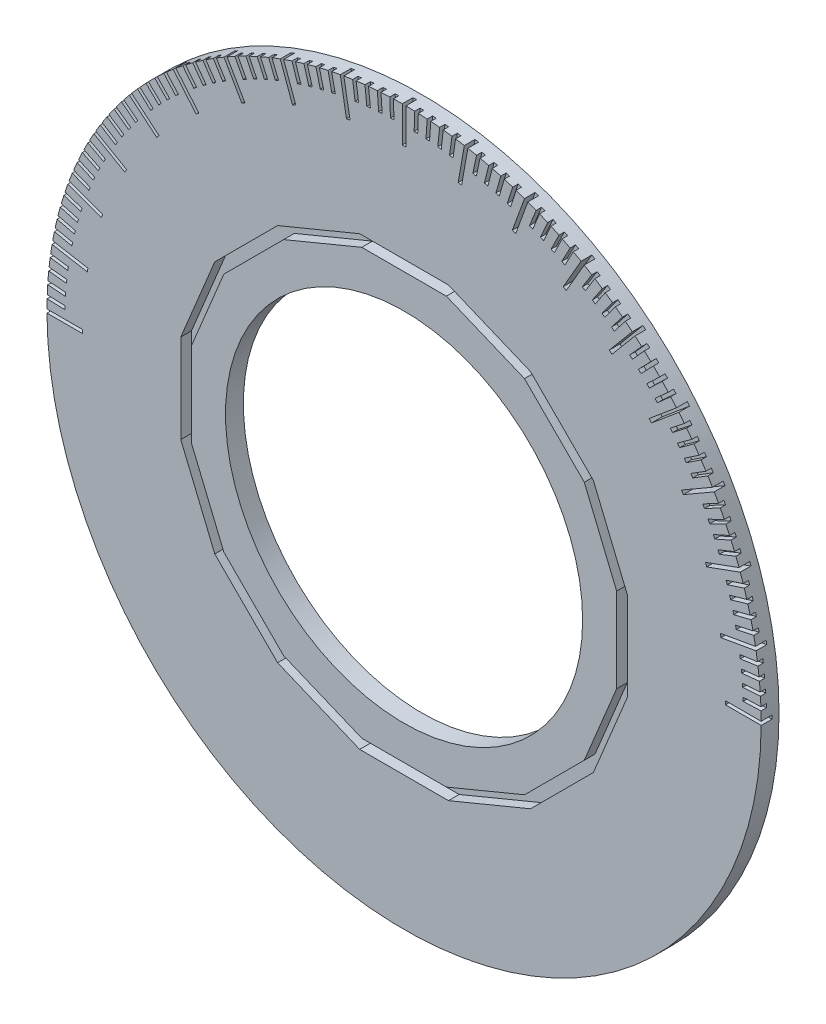
SolidWorks part; units mm, degrees
ref_plane "정면" through (0, 0, 0) normal (0, 0, 1) x (1, 0, 0)
ref_plane "윗면" through (0, 0, 0) normal (0, 1, 0) x (1, 0, 0)
ref_plane "우측면" through (0, 0, 0) normal (1, 0, 0) x (0, 0, -1)
sketch "스케치1" plane through (0, 0, 0) normal (0, 0, 1) x (1, 0, 0)
  circle A0 centre (0, 0) radius 40
  dimension "D1" = 80
extrude "보스-돌출1" add sketch "스케치1" along normal blind 2
sketch "스케치2" plane through (0, 0, 2) normal (0, 0, 1) x (1, 0, 0)
  line L103 (1.1, 0) -> (-1.1, 0) construction
  line L104 (21.2025, -14.167) -> (25.01, -4.9748)
  line L105 (25.01, -4.9748) -> (25.01, 4.9748)
  line L106 (25.01, 4.9748) -> (21.2025, 14.167)
  line L107 (21.2025, 14.167) -> (14.167, 21.2025)
  line L108 (14.167, 21.2025) -> (4.9748, 25.01)
  line L109 (4.9748, 25.01) -> (-4.9748, 25.01)
  line L110 (-4.9748, 25.01) -> (-14.167, 21.2025)
  line L111 (-14.167, 21.2025) -> (-21.2025, 14.167)
  line L112 (-21.2025, 14.167) -> (-25.01, 4.9748)
  line L113 (-25.01, 4.9748) -> (-25.01, -4.9748)
  line L114 (-25.01, -4.9748) -> (-21.2025, -14.167)
  line L115 (-21.2025, -14.167) -> (-14.167, -21.2025)
  line L116 (-14.167, -21.2025) -> (-4.9748, -25.01)
  line L117 (-4.9748, -25.01) -> (4.9748, -25.01)
  line L118 (4.9748, -25.01) -> (14.167, -21.2025)
  line L119 (14.167, -21.2025) -> (21.2025, -14.167)
  line L120 (20.1852, -13.4873) -> (23.81, -4.7361)
  line L121 (23.81, -4.7361) -> (23.81, 4.7361)
  line L122 (23.81, 4.7361) -> (20.1852, 13.4873)
  line L123 (20.1852, 13.4873) -> (13.4873, 20.1852)
  line L124 (13.4873, 20.1852) -> (4.7361, 23.81)
  line L125 (4.7361, 23.81) -> (-4.7361, 23.81)
  line L126 (-4.7361, 23.81) -> (-13.4873, 20.1852)
  line L127 (-13.4873, 20.1852) -> (-20.1852, 13.4873)
  line L128 (-20.1852, 13.4873) -> (-23.81, 4.7361)
  line L129 (-23.81, 4.7361) -> (-23.81, -4.7361)
  line L130 (-23.81, -4.7361) -> (-20.1852, -13.4873)
  line L131 (-20.1852, -13.4873) -> (-13.4873, -20.1852)
  line L132 (-13.4873, -20.1852) -> (-4.7361, -23.81)
  line L133 (-4.7361, -23.81) -> (4.7361, -23.81)
  line L134 (4.7361, -23.81) -> (13.4873, -20.1852)
  line L135 (13.4873, -20.1852) -> (20.1852, -13.4873)
  circle A0 centre (0, 0) radius 25.5 construction
  point P1 (0, 0)
  dimension "D1" = 51
  dimension "D2" = 1.2
extrude "컷-돌출1" cut sketch "스케치2" against normal blind 1.2
sketch "스케치7" plane through (0, 0, 2) normal (0, 0, 1) x (1, 0, 0)
  circle A0 centre (0, 0) radius 20
  dimension "D1" = 40
extrude "컷-돌출8" cut sketch "스케치7" against normal blind 22 contours A0
sketch "스케치8" plane through (0, 0, 2) normal (0, 0, 1) x (1, 0, 0)
  line L0 (-44.9996, 0) -> (-38, 0) construction
  line L1 (-40, 0.2) -> (-38, 0.2)
  line L3 (-40, 0.2) -> (-40, -0.2)
  line L4 (1.1, 0) -> (-1.1, 0) construction
  line L9 (-40, -0.2) -> (-38, -0.2)
  line L10 (-38, 0.2) -> (-38, -0.2)
  point P1092 (0, 0)
  dimension "D2" = 2
  dimension "D1" = 0.4
  dimension "D3" = 40
extrude "컷-돌출10" cut sketch "스케치8" against normal blind 0.6
pattern_circular "원형 패턴1" count 91 over 180 about axis through (0, 0, 0) along (0, 0, 1) of "컷-돌출10"
sketch "스케치10" plane through (0, 0, 2) normal (0, 0, 1) x (1, 0, 0)
  line L0 (-40, 0) -> (-36, 0) construction
  line L1 (-40, 0.2) -> (-36, 0.2)
  line L2 (-40, 0.2) -> (-40, -0.2)
  line L3 (-40, -0.2) -> (-36, -0.2)
  line L4 (-36, 0.2) -> (-36, -0.2)
  line L5 (1.1, 0) -> (-1.1, 0) construction
  dimension "D1" = 0.4
  dimension "D2" = 4
  dimension "D3" = 40
extrude "컷-돌출11" cut sketch "스케치10" against normal blind 1.2
pattern_circular "원형 패턴2" count 19 over 180 about axis through (0, 0, 0) along (0, 0, 1) of "컷-돌출11"
